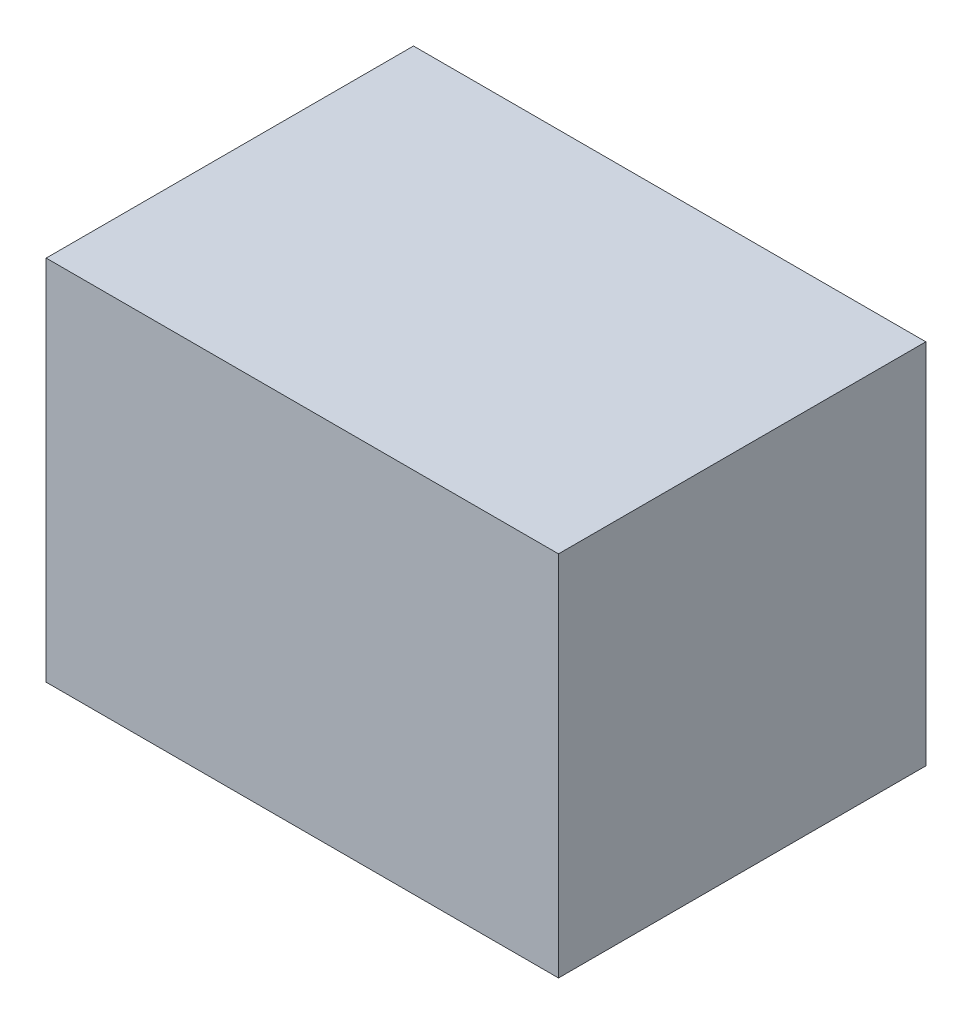
SolidWorks part; units mm, degrees
ref_plane "Front Plane" through (0, 0, 0) normal (0, 0, 1) x (1, 0, 0)
ref_plane "Top Plane" through (0, 0, 0) normal (0, 1, 0) x (1, 0, 0)
ref_plane "Right Plane" through (0, 0, 0) normal (1, 0, 0) x (0, 0, -1)
sketch "Sketch1" plane through (0, 0, 0) normal (0, 0, 1) x (1, 0, 0)
  line L1 (0, 0) -> (53, 0)
  line L2 (0, 0) -> (0, 38)
  line L3 (0, 38) -> (53, 38)
  line L4 (53, 0) -> (53, 38)
  dimension "D1" = 53
  dimension "D2" = 38
extrude "Boss-Extrude1" add sketch "Sketch1" along normal blind 38
